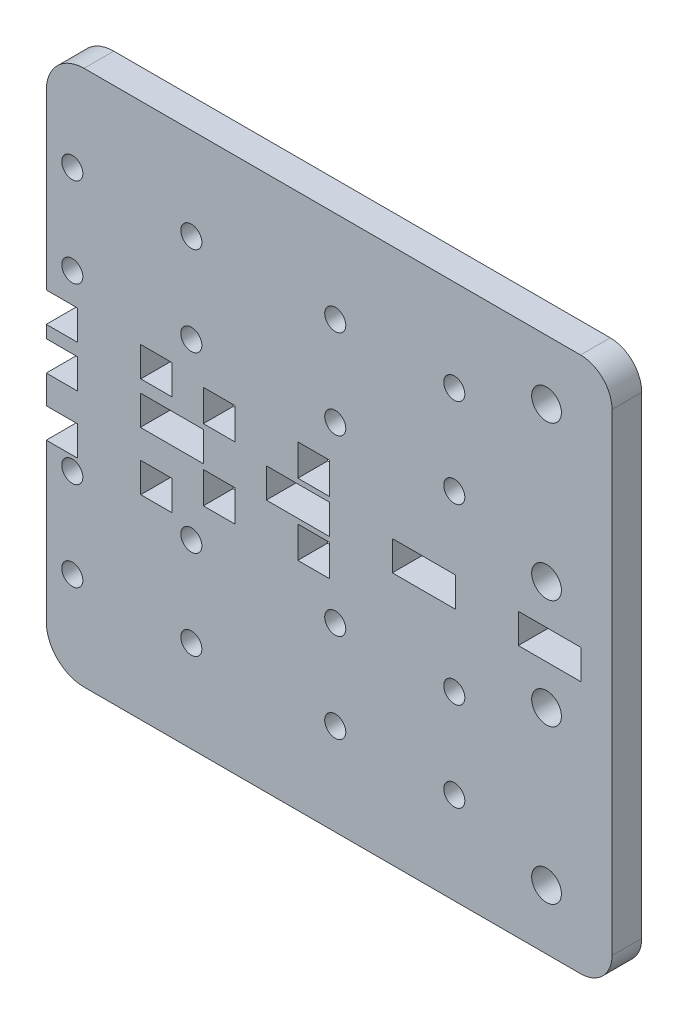
SolidWorks part; units mm, degrees
ref_plane "Front Plane" through (0, 0, 0) normal (0, 0, 1) x (1, 0, 0)
ref_plane "Top Plane" through (0, 0, 0) normal (0, 1, 0) x (1, 0, 0)
ref_plane "Right Plane" through (0, 0, 0) normal (1, 0, 0) x (0, 0, -1)
sketch "Sketch1" plane through (0, 0, 0) normal (0, 0, 1) x (-1, 0, 0)
  line L0 (70.7026, 1.6661) -> (72.0987, 1.6661)
  line L1 (70.7026, -4.3283) -> (72.0987, -4.3283)
  line L2 (72.0987, -4.3283) -> (72.0987, -6.8406)
  line L3 (72.0987, -12.8406) -> (72.0987, -47.7342)
  line L4 (46.6987, 13.3834) -> (53.0487, 13.3834)
  line L5 (46.6987, 13.3834) -> (46.6987, 7.3834)
  line L6 (46.6987, 7.3834) -> (53.0487, 7.3834)
  line L7 (72.0987, -12.8406) -> (72.0987, -42.8406)
  line L8 (-15.4204, 10.1785) -> (-15.4204, -12.8406) construction
  line L9 (-35.7704, 4.6785) -> (-35.7704, 45.6785) construction
  line L10 (-35.7704, 45.6785) -> (-21.7704, 45.6785) construction
  line L11 (-21.7704, 45.6785) -> (-21.7704, 4.6785) construction
  line L12 (-21.7704, 4.6785) -> (-35.7704, 4.6785) construction
  line L13 (-1015.4204, -1.3311) -> (48984.5796, -1.3311) construction
  line L14 (-35.7704, 1.6661) -> (-23.0704, 1.6661)
  line L15 (-21.7704, -7.3406) -> (-35.7704, -7.3406) construction
  line L16 (-21.7704, -48.3406) -> (-21.7704, -7.3406) construction
  line L17 (-35.7704, -48.3406) -> (-21.7704, -48.3406) construction
  line L18 (-35.7704, -7.3406) -> (-35.7704, -48.3406) construction
  line L19 (53.0487, 13.3834) -> (53.0487, 7.3834)
  line L20 (45.3026, 52.6921) -> (64.4787, 52.6921)
  line L21 (72.0987, 45.0721) -> (72.0987, 13.3834)
  line L22 (64.4787, -55.3542) -> (45.3026, -55.3542)
  line L23 (65.7487, 13.3834) -> (72.0987, 13.3834)
  line L24 (65.7487, 13.3834) -> (65.7487, 7.3834)
  line L25 (65.7487, 7.3834) -> (72.0987, 7.3834)
  line L27 (46.6987, -6.8406) -> (53.0487, -6.8406)
  line L28 (46.6987, -6.8406) -> (46.6987, -12.8406)
  line L29 (-10.3704, 1.6661) -> (2.3296, 1.6661)
  line L30 (19.9026, 52.6921) -> (45.3026, 52.6921)
  line L31 (15.0296, 1.6661) -> (27.7296, 1.6661)
  line L32 (-964.4397, 2.6689) -> (49035.5603, 2.6689) construction
  line L33 (-964.4397, -5.3311) -> (49035.5603, -5.3311) construction
  line L34 (40.4296, 1.6661) -> (53.1296, 1.6661)
  line L35 (65.8296, 1.6661) -> (70.7026, 1.6661)
  line L36 (15.0296, 2.6689) -> (15.0296, 9.0189)
  line L37 (15.0296, 9.0189) -> (21.3796, 9.0189)
  line L38 (15.0296, 2.6689) -> (21.3796, 2.6689)
  line L39 (19.9026, 52.6921) -> (-35.6234, 52.6921)
  line L40 (40.4296, -5.3311) -> (40.4296, -11.6811)
  line L41 (34.0796, -5.3311) -> (40.4296, -5.3311)
  line L42 (34.0796, -11.6811) -> (40.4296, -11.6811)
  line L43 (34.0796, -5.3311) -> (34.0796, -11.6811)
  line L44 (-35.7704, -4.3283) -> (-35.7704, 1.6661)
  line L45 (21.3796, 2.6689) -> (21.3796, 9.0189)
  line L46 (-23.0704, 1.6661) -> (-23.0704, -4.3283)
  line L47 (21.3796, -5.3311) -> (21.3796, -11.6811)
  line L48 (-10.3704, -4.3283) -> (-10.3704, 1.6661)
  line L49 (34.0796, 2.6689) -> (34.0796, 9.0189)
  line L50 (34.0796, 9.0189) -> (40.4296, 9.0189)
  line L51 (19.9026, -55.3542) -> (-35.6234, -55.3542)
  line L52 (-41.9734, 46.3421) -> (-41.9734, -49.0042)
  line L53 (34.0796, 2.6689) -> (40.4296, 2.6689)
  line L54 (2.3296, 1.6661) -> (2.3296, -4.3283)
  line L55 (15.0296, -5.3311) -> (21.3796, -5.3311)
  line L56 (15.0296, -4.3283) -> (15.0296, 1.6661)
  line L57 (40.4296, 2.6689) -> (40.4296, 9.0189)
  line L58 (27.7296, 1.6661) -> (27.7296, -4.3283)
  line L59 (15.0296, -11.6811) -> (21.3796, -11.6811)
  line L60 (40.4296, -4.3283) -> (40.4296, 1.6661)
  line L61 (46.6987, -12.8406) -> (53.0487, -12.8406)
  line L62 (53.1296, 1.6661) -> (53.1296, -4.3283)
  line L63 (15.0296, -5.3311) -> (15.0296, -11.6811)
  line L64 (65.8296, -4.3283) -> (65.8296, 1.6661)
  line L65 (53.0487, -6.8406) -> (53.0487, -12.8406)
  line L66 (65.8296, -4.3283) -> (70.7026, -4.3283)
  line L67 (40.4296, -4.3283) -> (53.1296, -4.3283)
  line L68 (15.0296, -4.3283) -> (27.7296, -4.3283)
  line L69 (-10.3704, -4.3283) -> (2.3296, -4.3283)
  line L70 (-35.7704, -4.3283) -> (-23.0704, -4.3283)
  line L71 (19.9026, -55.3542) -> (45.3026, -55.3542)
  line L72 (65.7487, -6.8406) -> (72.0987, -6.8406)
  line L73 (65.7487, -6.8406) -> (65.7487, -12.8406)
  line L74 (65.7487, -12.8406) -> (72.0987, -12.8406)
  line L75 (72.0987, 7.3834) -> (72.0987, 1.6661)
  line L96 (72.0987, 40.1785) -> (72.0987, 13.3834)
  arc A0 (-35.6234, 52.6921) -> (-41.9734, 46.3421) centre (-35.6234, 46.3421) ccw
  circle A1 centre (-10.1704, -18.8406) radius 2.125
  circle A2 centre (66.8487, -36.8406) radius 2.125
  circle A3 centre (42.8487, -18.8406) radius 2.125
  circle A4 centre (-28.7704, -43.3406) radius 3
  circle A5 centre (-28.7704, -12.3406) radius 3
  circle A6 centre (13.8296, -18.8406) radius 2.125
  circle A7 centre (42.8487, -36.8406) radius 2.125
  circle A8 centre (-10.1704, -36.8406) radius 2.125
  circle A9 centre (66.8487, -18.8406) radius 2.125
  circle A10 centre (13.8296, -36.8406) radius 2.125
  arc A11 (64.4787, 52.6921) -> (72.0987, 45.0721) centre (64.4787, 45.0721) cw
  circle A12 centre (-28.7704, 9.6785) radius 3
  arc A13 (72.0987, -47.7342) -> (64.4787, -55.3542) centre (64.4787, -47.7342) cw
  circle A14 centre (-28.7704, 40.6785) radius 3
  arc A19 (-35.6234, -55.3542) -> (-41.9734, -49.0042) centre (-35.6234, -49.0042) cw
  circle A24 centre (-10.1704, 34.1785) radius 2.125
  circle A25 centre (13.8296, 34.1785) radius 2.125
  circle A26 centre (13.8296, 16.1785) radius 2.125
  circle A27 centre (-10.1704, 16.1785) radius 2.125
  circle A28 centre (42.8487, 34.1785) radius 2.125
  circle A29 centre (66.8487, 34.1785) radius 2.125
  circle A30 centre (66.8487, 16.1785) radius 2.125
  circle A31 centre (42.8487, 16.1785) radius 2.125
  point P42 (-15.4204, -1.3311)
  dimension "D11" = 6.35
  dimension "D2" = 7.62
  dimension "D3" = 7.62
  dimension "D5" = 23.0192
  dimension "D12" = 4
extrude "Boss-Extrude1" add sketch "Sketch1" along normal blind 5.9944
